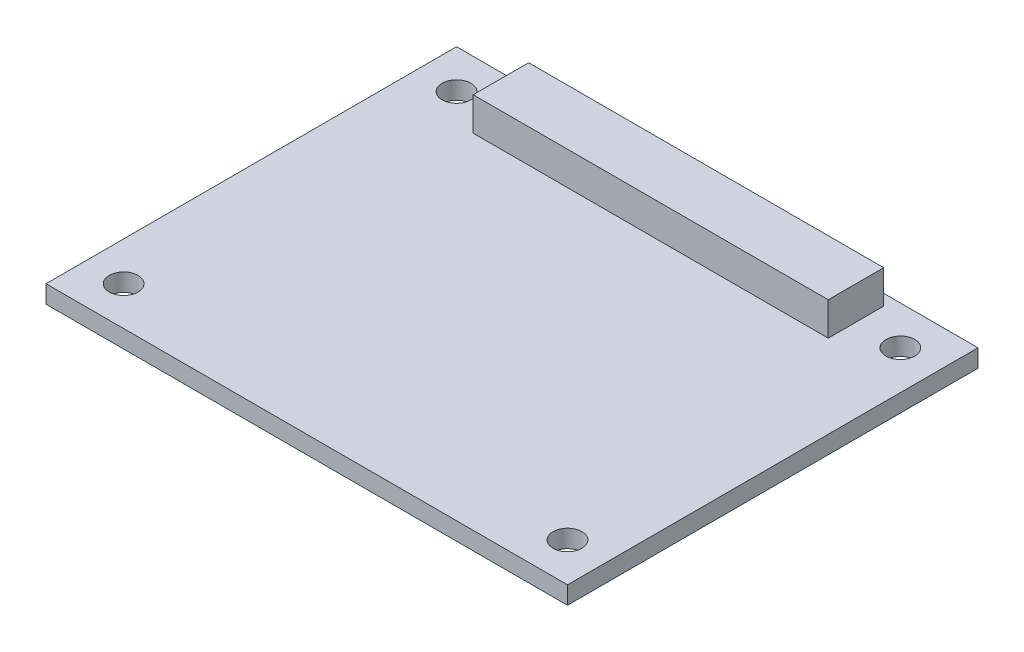
SolidWorks part; units mm, degrees
ref_plane "Front" through (0, 0, 0) normal (0, 0, 1) x (1, 0, 0)
ref_plane "Top" through (0, 0, 0) normal (0, 1, 0) x (1, 0, 0)
ref_plane "Right" through (0, 0, 0) normal (1, 0, 0) x (0, 0, -1)
sketch "Эскиз1" plane through (0, 0, 0) normal (0, 1, 0) x (1, 0, 0)
  line L1 (23.5, -18.5) -> (-23.5, -18.5)
  line L2 (23.5, -18.5) -> (23.5, 18.5)
  line L3 (23.5, 18.5) -> (-23.5, 18.5)
  line L4 (-23.5, -18.5) -> (-23.5, 18.5)
  line L5 (23.5, -18.5) -> (-23.5, 18.5) construction
  line L6 (23.5, 18.5) -> (-23.5, -18.5) construction
  point P0 (0, 0)
  dimension "D1" = 37
  dimension "D2" = 47
extrude "Бобышка-Вытянуть1" add sketch "Эскиз1" against normal blind 1.6
sketch "Эскиз2" plane through (0, 0, 0) normal (0, 1, 0) x (1, 0, 0)
  line L1 (20, -15) -> (-20, -15) construction
  line L2 (20, -15) -> (20, 15) construction
  line L3 (20, 15) -> (-20, 15) construction
  line L4 (-20, -15) -> (-20, 15) construction
  line L5 (20, -15) -> (-20, 15) construction
  line L6 (20, 15) -> (-20, -15) construction
  circle A0 centre (-20, 15) radius 1.3
  circle A1 centre (-20, -15) radius 1.3
  circle A2 centre (20, -15) radius 1.3
  circle A3 centre (20, 15) radius 1.3
  point P0 (0, 0)
  dimension "D1" = 30
  dimension "D2" = 40
extrude "Вырез-Вытянуть1" cut sketch "Эскиз2" against normal blind 1.6
sketch "Эскиз3" plane through (0, 0, 0) normal (0, 1, 0) x (1, 0, 0)
  line L0 (0, 0) -> (0, 24.5475) construction
  line L1 (16, 12.5) -> (-16, 12.5)
  line L2 (16, 12.5) -> (16, 17.5)
  line L3 (16, 17.5) -> (-16, 17.5)
  line L4 (-16, 12.5) -> (-16, 17.5)
  line L5 (16, 12.5) -> (-16, 17.5) construction
  line L6 (16, 17.5) -> (-16, 12.5) construction
  line L7 (23.5, 18.5) -> (-23.5, 18.5) construction
  point P0 (0, 15)
  dimension "D1" = 5
  dimension "D2" = 32
  dimension "D3" = 1
extrude "Бобышка-Вытянуть2" add sketch "Эскиз3" along normal blind 3
sketch "Эскиз4" plane through (0, 0, 0) normal (0, 1, 0) x (1, 0, 0)
  line L7 (-17.1047, -11.6521) -> (-8.1047, -11.6521)
  line L8 (-17.1047, -11.6521) -> (-17.1047, -2.6521)
  line L9 (-17.1047, -2.6521) -> (-8.1047, -2.6521)
  line L10 (-8.1047, -11.6521) -> (-8.1047, -2.6521)
  line L11 (-17.1047, -11.6521) -> (-8.1047, -2.6521) construction
  line L12 (-17.1047, -2.6521) -> (-8.1047, -11.6521) construction
  point P0 (-12.3, -7.25)
  point P5 (-12.6047, -7.1521)
  dimension "D1" = 12.3
  dimension "D2" = 7.25
  dimension "D3" = 9
  dimension "D4" = 9
